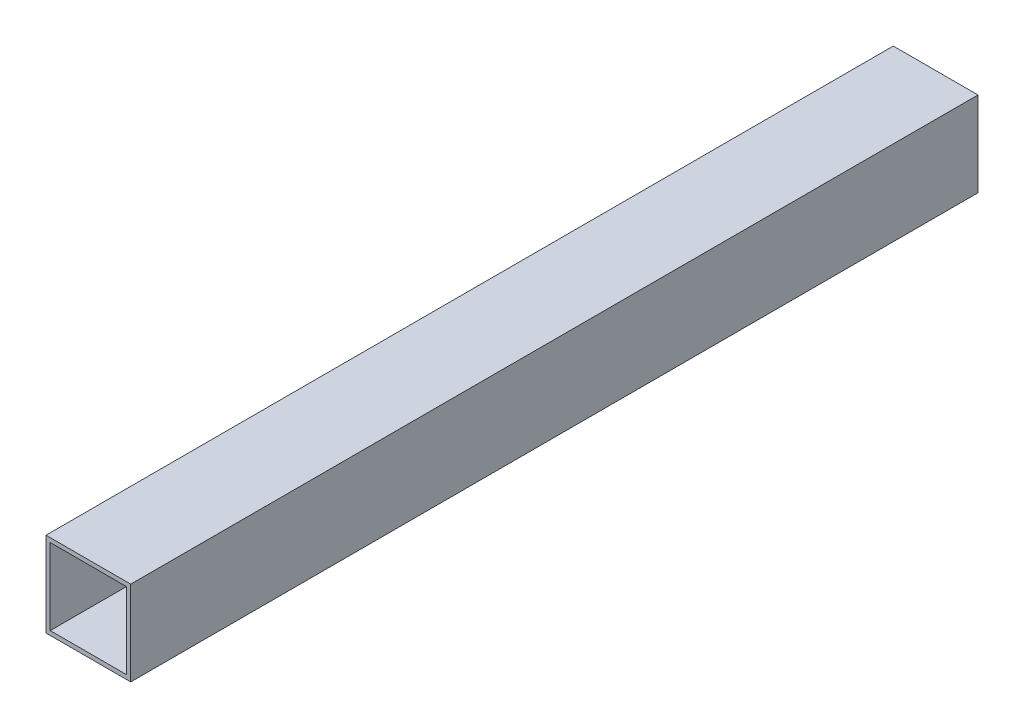
SolidWorks part; units mm, degrees
material "Plain Carbon Steel"
ref_plane "Front Plane" through (0, 0, 0) normal (0, 0, 1) x (1, 0, 0)
ref_plane "Top Plane" through (0, 0, 0) normal (0, 1, 0) x (1, 0, 0)
ref_plane "Right Plane" through (0, 0, 0) normal (1, 0, 0) x (0, 0, -1)
sketch "Sketch1" plane through (0, 0, 0) normal (0, 0, 1) x (1, 0, 0)
  line B0 (-50, -50) -> (50, -50)
  line B1 (-50, -50) -> (-50, 50)
  line B2 (50, -50) -> (50, 50)
  line B3 (-50, 50) -> (50, 50)
  line B4 (-45, -45) -> (45, -45)
  line B5 (-45, -45) -> (-45, 45)
  line B6 (45, -45) -> (45, 45)
  line B7 (-45, 45) -> (45, 45)
sketch_block_instance "10x10x5_profil-1"
sketch_block "10x10x5_profil" parameters "D1"=100, "D2"=100, "D3"=5, "D4"=5
extrude "Boss-Extrude1" add sketch "Sketch1" along normal mid plane 1000
